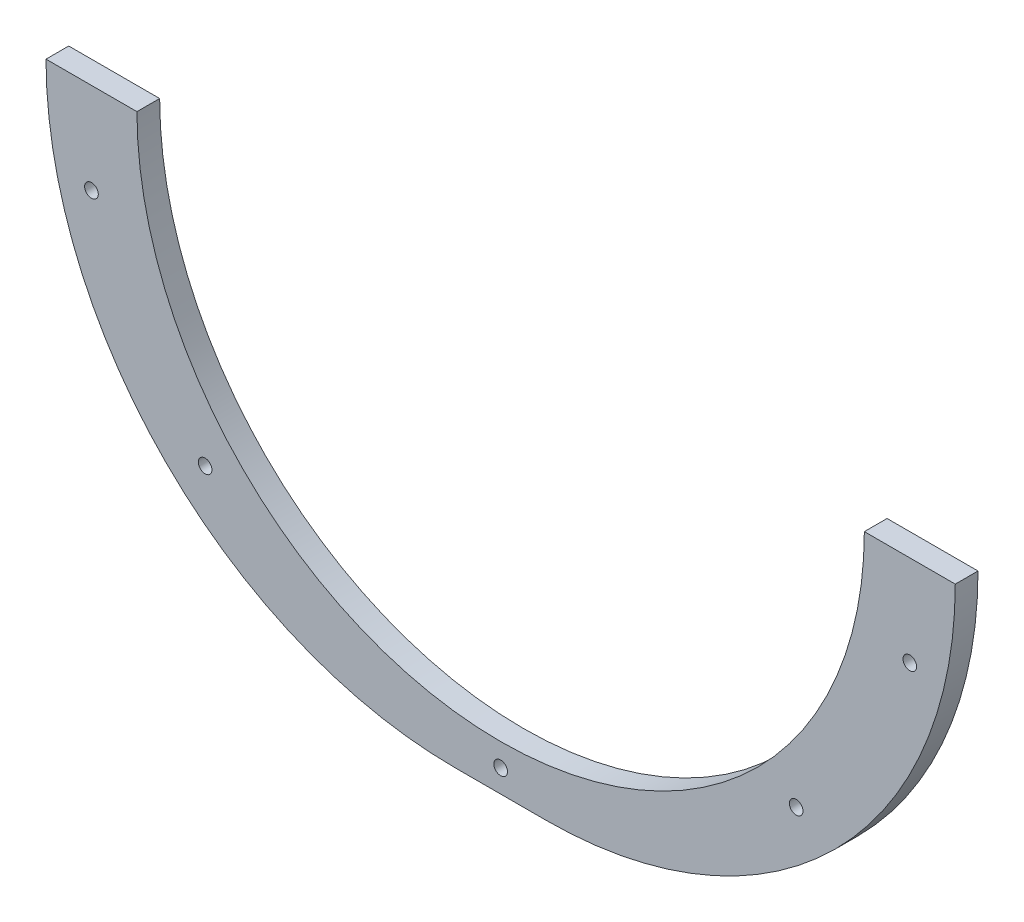
SolidWorks part; units mm, degrees
material "Acrílico (médio-alto impacto)"
ref_plane "Plano frontal" through (0, 0, 0) normal (0, 0, 1) x (1, 0, 0)
ref_plane "Plano superior" through (0, 0, 0) normal (0, 1, 0) x (1, 0, 0)
ref_plane "Plano direito" through (0, 0, 0) normal (1, 0, 0) x (0, 0, -1)
sketch "Esboço1" plane through (0, 0, 0) normal (0, 0, 1) x (1, 0, 0)
  line L0 (-16.5205, -40.7692) -> (3.4795, -40.7692)
  line L1 (93.4795, -130.7692) -> (73.4795, -130.7692)
  line L2 (163.4795, -40.7692) -> (183.4795, -40.7692)
  line L9 (183.4795, -105.7692) -> (178.4795, -105.7692) construction
  line L10 (183.4795, -105.7692) -> (183.4795, -40.7692) construction
  line L12 (178.4795, -105.7692) -> (178.4795, -70.3496) construction
  line L13 (158.4795, -130.7692) -> (8.4795, -130.7692) construction
  line L14 (158.4795, -130.7692) -> (158.4795, -125.7692) construction
  line L15 (158.4795, -125.7692) -> (8.4795, -125.7692) construction
  line L16 (8.4795, -130.7692) -> (8.4795, -125.7692) construction
  line L17 (-16.5205, -105.7692) -> (-11.5205, -105.7692) construction
  line L18 (-16.5205, -105.7692) -> (-16.5205, -40.7692) construction
  line L20 (-11.5205, -105.7692) -> (-11.5205, -70.3496) construction
  line L22 (83.4795, -130.7692) -> (83.4795, -125.7692) construction
  arc A0 (3.4795, -40.7692) -> (163.4795, -40.7692) centre (83.4795, -40.7692) ccw
  arc A1 (183.4795, -40.7692) -> (93.4795, -130.7692) centre (93.4795, -40.7692) cw
  arc A2 (73.4795, -130.7692) -> (-16.5205, -40.7692) centre (73.4795, -40.7692) cw
  dimension "D6" = 160
  dimension "D13" = 90
  dimension "D5" = 90
  dimension "D2" = 5
  dimension "D3" = 5
  dimension "D4" = 5
extrude "Ressalto-extrusão1" add sketch "Esboço1" along normal blind 5
sketch "Esboço2" plane through (0, 0, 5) normal (0, 0, 1) x (1, 0, 0)
  line L0 (73.4795, -130.7692) -> (93.4795, -130.7692) construction
  line L1 (83.4795, -97.7761) -> (83.4795, -105.1094) construction
  circle A0 centre (83.4795, -125.7692) radius 1.5
  circle A1 centre (148.4795, -100.7692) radius 1.5
  circle A2 centre (173.4795, -60.7692) radius 1.5
  circle A3 centre (-6.5205, -60.7692) radius 1.5
  circle A4 centre (18.4795, -100.7692) radius 1.5
  dimension "D1" = 100
  dimension "D2" = 5
  dimension "D3" = 3
  dimension "D4" = 3
  dimension "D5" = 3
  dimension "D6" = 35
  dimension "D7" = 30
  dimension "D8" = 70
  dimension "D9" = 10
extrude "Corte-extrusão1" cut sketch "Esboço2" against normal blind 10
